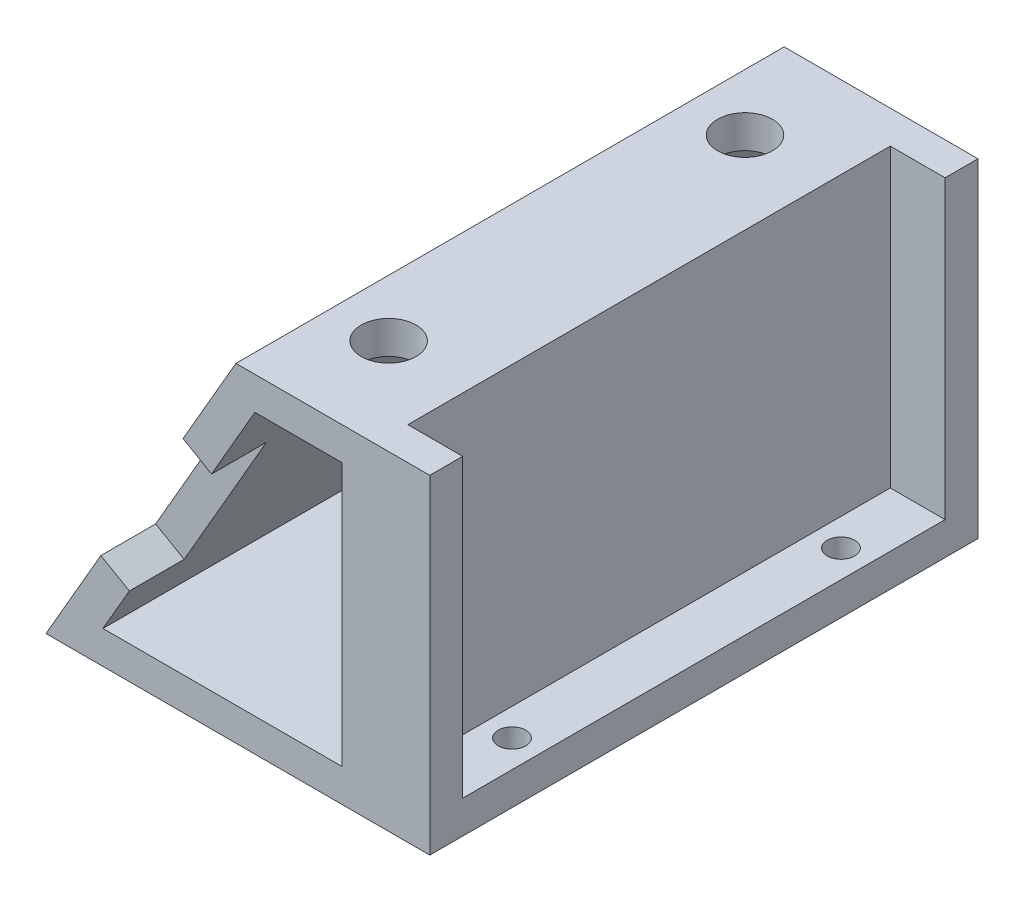
SolidWorks part; units mm, degrees
ref_plane "Ebene vorne" through (0, 0, 0) normal (0, 0, 1) x (1, 0, 0)
ref_plane "Ebene oben" through (0, 0, 0) normal (0, 1, 0) x (1, 0, 0)
ref_plane "Ebene rechts" through (0, 0, 0) normal (1, 0, 0) x (0, 0, -1)
sketch "Skizze2" plane through (0, 0, 0) normal (0, 0, 1) x (1, 0, 0)
  line L0 (-21.4907, -15.9499) -> (-4.1701, 14.0501)
  line L1 (-21.4907, 14.0501) -> (13.5093, 14.0501)
  line L2 (-21.4907, 14.0501) -> (-21.4907, -15.9499)
  line L3 (-21.4907, -15.9499) -> (13.5093, -15.9499)
  line L4 (13.5093, 14.0501) -> (13.5093, -15.9499)
  line L5 (-16.2945, -12.9499) -> (-2.4381, 11.0501)
  line L6 (-2.4381, 11.0501) -> (5.5093, 11.0501)
  line L7 (5.5093, 11.0501) -> (5.5093, -12.9499)
  line L8 (5.5093, -12.9499) -> (-16.2945, -12.9499)
  dimension "D1" = 30
  dimension "D2" = 35
  dimension "D3" = 60
  dimension "D4" = 3
  dimension "D5" = 3
  dimension "D6" = 3
  dimension "D7" = 0
  dimension "D8" = 8
extrude "Aufsatz-Linear austragen1" add sketch "Skizze2" along normal blind 50 contours L4 L1 L0 L3 L7 L8 L5 L6
sketch "Skizze3" plane through (0, -15.9499, 0) normal (0, -1, 0) x (1, 0, 0)
  line L0 (13.5093, 50) -> (13.5093, 0) construction
  line L2 (-21.4907, 0) -> (13.5093, 0) construction
  line L3 (-21.4907, 50) -> (13.5093, 50) construction
  circle A0 centre (11.0093, 40) radius 1.25
  circle A1 centre (11.0093, 10) radius 1.25
  circle A2 centre (1.0093, 41.25) radius 1.5
  circle A3 centre (1.0093, 8.75) radius 1.5
  dimension "D2" = 2.5
  dimension "D3" = 2.5
  dimension "D4" = 2.5
  dimension "D7" = 3
  dimension "D8" = 3
  dimension "D1" = 2.5
  dimension "D5" = 10
  dimension "D6" = 30
  dimension "D9" = 8.75
  dimension "D10" = 32.5
  dimension "D11" = 10
  dimension "D12" = 10
extrude "Schnitt-Linear austragen1" cut sketch "Skizze3" against normal blind 3
sketch "Skizze4" plane through (0, 14.0501, 0) normal (0, 1, 0) x (1, 0, 0)
  line L0 (-4.1701, -50) -> (13.5093, -50) construction
  line L1 (13.5093, -3) -> (8.5093, -3)
  line L2 (13.5093, -3) -> (13.5093, -47)
  line L3 (13.5093, -47) -> (8.5093, -47)
  line L4 (8.5093, -3) -> (8.5093, -47)
  line L5 (-4.1701, 0) -> (13.5093, 0) construction
  line L6 (13.5093, -50) -> (13.5093, 0) construction
  dimension "D1" = 3
  dimension "D2" = 3
  dimension "D3" = 0
  dimension "D4" = 5
extrude "Schnitt-Linear austragen2" cut sketch "Skizze4" against normal blind 27
sketch "Skizze5" plane through (0, 14.0501, 0) normal (0, 1, 0) x (1, 0, 0)
  line L0 (-4.1701, -50) -> (13.5093, -50) construction
  line L1 (13.5093, -50) -> (13.5093, -47) construction
  line L2 (13.5093, -3) -> (13.5093, 0) construction
  circle A0 centre (1.0093, -41.25) radius 2.5
  circle A1 centre (1.0093, -8.75) radius 2.5
  dimension "D1" = 5
  dimension "D2" = 5
  dimension "D3" = 8.75
  dimension "D4" = 12.5
  dimension "D5" = 32.5
  dimension "D6" = 12.5
extrude "Schnitt-Linear austragen3" cut sketch "Skizze5" against normal blind 28
sketch "Skizze6" plane through (-9.2115, 5.3183, 0) normal (-0.866, 0.5, 0) x (0, 0, 1)
  line L0 (50, 10.0827) -> (0, 10.0827) construction
  line L1 (0, -24.5583) -> (0, 10.0827) construction
  circle A0 centre (35, -1.9173) radius 1.25
  circle A1 centre (15, -1.9173) radius 1.25
  dimension "D2" = 2.5
  dimension "D3" = 2.5
  dimension "D1" = 12
  dimension "D4" = 12
  dimension "D5" = 20
  dimension "D6" = 15
extrude "Schnitt-Linear austragen4" cut sketch "Skizze6" against normal blind 3
sketch "Skizze7" plane through (-9.2115, 5.3183, 0) normal (-0.866, 0.5, 0) x (0, 0, 1)
  line L0 (0, -24.5583) -> (0, 10.0827) construction
  line L1 (45, 0.4417) -> (50, 0.4417)
  line L2 (45, 0.4417) -> (45, -14.5583)
  line L3 (45, -14.5583) -> (50, -14.5583)
  line L4 (50, 0.4417) -> (50, -14.5583)
  line L5 (0, 0.4417) -> (5, 0.4417)
  line L6 (0, 0.4417) -> (0, -14.5583)
  line L7 (0, -14.5583) -> (5, -14.5583)
  line L8 (5, 0.4417) -> (5, -14.5583)
  line L9 (50, -24.5583) -> (50, 10.0827) construction
  line L10 (50, -24.5583) -> (0, -24.5583) construction
  dimension "D1" = 15
  dimension "D2" = 5
  dimension "D3" = 5
  dimension "D4" = 15
  dimension "D5" = 0
  dimension "D6" = 0
  dimension "D7" = 10
  dimension "D8" = 10
extrude "Schnitt-Linear austragen5" cut sketch "Skizze7" against normal blind 3
